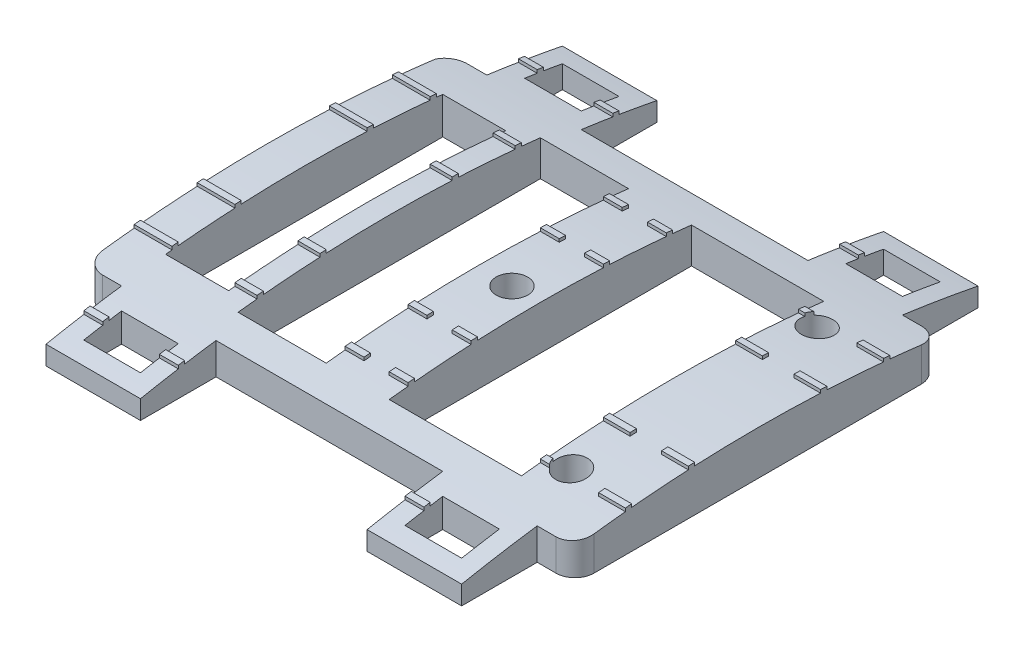
SolidWorks part; units mm, degrees
ref_plane "Front Plane" through (0, 0, 0) normal (0, 0, 1) x (1, 0, 0)
ref_plane "Top Plane" through (0, 0, 0) normal (0, 1, 0) x (1, 0, 0)
ref_plane "Right Plane" through (0, 0, 0) normal (1, 0, 0) x (0, 0, -1)
sketch "Sketch1" plane through (0, 0, 0) normal (0, 1, 0) x (1, 0, 0)
  line L0 (-33, -29) -> (-33, -41) construction
  line L5 (-33, -41) -> (-18, -41) construction
  line L6 (-18, -29) -> (-18, -41) construction
  line L7 (18, -29) -> (18, -41) construction
  line L8 (33, -41) -> (18, -41) construction
  line L9 (33, -29) -> (33, -41) construction
  line L10 (18, 29) -> (18, 41) construction
  line L11 (33, 41) -> (18, 41) construction
  line L12 (33, 29) -> (33, 41) construction
  line L13 (-33, 29) -> (-33, 41) construction
  line L14 (-33, 41) -> (-18, 41) construction
  line L15 (-18, 29) -> (-18, 41) construction
  line L16 (-36.1131, 29) -> (-33, 29) construction
  line L17 (-33, 29) -> (-18, 29) construction
  line L18 (-18, 29) -> (18, 29) construction
  line L19 (18, 29) -> (33, 29) construction
  line L20 (33, 29) -> (36, 29) construction
  line L21 (-36, -29) -> (-33, -29) construction
  line L34 (-18, -29) -> (-33, -29) construction
  line L35 (-18, -29) -> (18, -29) construction
  line L36 (33, -29) -> (18, -29) construction
  line L38 (33, -29) -> (36, -29) construction
  line L40 (-33, -29) -> (-33, -41)
  line L44 (-33, -41) -> (-18, -41)
  line L45 (-18, -29) -> (-18, -41)
  line L49 (18, -29) -> (18, -41)
  line L60 (33, -41) -> (18, -41)
  line L94 (33, -29) -> (33, -41)
  line L95 (18, 29) -> (18, 41)
  line L96 (33, 41) -> (18, 41)
  line L97 (33, 29) -> (33, 41)
  line L98 (-33, 29) -> (-33, 41)
  line L99 (-33, 41) -> (-18, 41)
  line L100 (-18, 29) -> (-18, 41)
  line L101 (-36.1131, 29) -> (-33, 29)
  line L102 (-33, 29) -> (-18, 29)
  line L103 (-18, 29) -> (18, 29)
  line L104 (18, 29) -> (33, 29)
  line L105 (33, 29) -> (36, 29)
  line L106 (-36, -29) -> (-33, -29)
  line L107 (-18, -29) -> (-33, -29)
  line L108 (-18, -29) -> (18, -29)
  line L109 (33, -29) -> (18, -29)
  line L110 (33, -29) -> (36, -29)
  line L111 (-39, -26) -> (-39, 26.8161)
  line L112 (39, -26) -> (39, 26)
  line L113 (-30, -32) -> (-30, -38) construction
  line L114 (-30, -38) -> (-21, -38) construction
  line L115 (-21, -32) -> (-21, -38) construction
  line L116 (-30, -32) -> (-21, -32) construction
  line L117 (21, -32) -> (21, -38) construction
  line L118 (30, -38) -> (21, -38) construction
  line L119 (30, -32) -> (21, -32) construction
  line L120 (30, -32) -> (30, -38) construction
  line L121 (-30, 32) -> (-21, 32) construction
  line L122 (-30, 32) -> (-30, 38) construction
  line L123 (-30, 38) -> (-21, 38) construction
  line L124 (-21, 32) -> (-21, 38) construction
  line L125 (21, 32) -> (21, 38) construction
  line L126 (30, 32) -> (21, 32) construction
  line L127 (30, 32) -> (30, 38) construction
  line L128 (30, 38) -> (21, 38) construction
  line L129 (-30, -32) -> (-30, -38)
  line L130 (-30, -38) -> (-21, -38)
  line L131 (-21, -32) -> (-21, -38)
  line L132 (-30, -32) -> (-21, -32)
  line L133 (21, -32) -> (21, -38)
  line L134 (30, -38) -> (21, -38)
  line L135 (30, -32) -> (21, -32)
  line L136 (30, -32) -> (30, -38)
  line L137 (-30, 32) -> (-21, 32)
  line L138 (-30, 32) -> (-30, 38)
  line L139 (-30, 38) -> (-21, 38)
  line L140 (-21, 32) -> (-21, 38)
  line L141 (21, 32) -> (21, 38)
  line L142 (30, 32) -> (21, 32)
  line L143 (30, 32) -> (30, 38)
  line L144 (30, 38) -> (21, 38)
  arc A0 (-36.1131, 29) -> (-39.0792, 26.45) centre (-36.1131, 26) ccw construction
  arc A1 (39, 26) -> (36, 29) centre (36, 26) ccw construction
  arc A2 (-39, -26) -> (-36, -29) centre (-36, -26) ccw construction
  arc A3 (36, -29) -> (39, -26) centre (36, -26) ccw construction
  arc A6 (-36.1131, 29) -> (-39, 26.8161) centre (-36.1131, 26) ccw
  arc A7 (39, 26) -> (36, 29) centre (36, 26) ccw
  arc A8 (-39, -26) -> (-36, -29) centre (-36, -26) ccw
  arc A9 (36, -29) -> (39, -26) centre (36, -26) ccw
extrude "Boss-Extrude1" add sketch "Sketch1" along normal blind 10
sketch "Sketch7" plane through (0, 0, 0) normal (0, -1, 0) x (1, 0, 0)
  circle A1 centre (28.95, 19.5) radius 2.5
  circle A3 centre (28.95, -19.5) radius 2.5
  circle A5 centre (0, 0) radius 2.5
  circle A8 centre (0, 0) radius 2 construction
  dimension "D1" = 0.5
extrude "Cut-Extrude6" cut sketch "Sketch7" against normal through all
sketch "Sketch8" plane through (0, 0, 0) normal (0, -1, 0) x (1, 0, 0)
  line L0 (-24, 21) -> (-32, -21) construction
  line L1 (-24, 21) -> (-32, 21) construction
  line L2 (-24, 21) -> (-24, -21) construction
  line L3 (-24, -21) -> (-32, -21) construction
  line L4 (-32, 21) -> (-32, -21) construction
  line L5 (-24, 21) -> (-32, -21) construction
  line L6 (-24, -21) -> (-32, 21) construction
  line L7 (5.5, -23) -> (24.5, 23) construction
  line L8 (-6.5, 23) -> (-18.5, 23) construction
  line L9 (-6.5, 23) -> (-6.5, -23) construction
  line L10 (-6.5, -23) -> (-18.5, -23) construction
  line L11 (-18.5, 23) -> (-18.5, -23) construction
  line L12 (-6.5, 23) -> (-18.5, -23) construction
  line L13 (-6.5, -23) -> (-18.5, 23) construction
  line L14 (24.5, 23) -> (5.5, 23) construction
  line L15 (24.5, 23) -> (24.5, -23) construction
  line L16 (24.5, -23) -> (5.5, -23) construction
  line L17 (5.5, 23) -> (5.5, -23) construction
  line L18 (24.5, 23) -> (5.5, -23) construction
  line L19 (24.5, -23) -> (5.5, 23) construction
  line L20 (25.5, -24) -> (4.5, -24)
  line L21 (4.5, 24) -> (4.5, -24)
  line L22 (25.5, 24) -> (4.5, 24)
  line L23 (25.5, 24) -> (25.5, -24)
  line L24 (-5.5, -24) -> (-19.5, -24)
  line L25 (-19.5, 24) -> (-19.5, -24)
  line L26 (-5.5, 24) -> (-19.5, 24)
  line L27 (-5.5, 24) -> (-5.5, -24)
  line L28 (-23, -22) -> (-33, -22)
  line L29 (-33, 22) -> (-33, -22)
  line L30 (-23, 22) -> (-33, 22)
  line L31 (-23, 22) -> (-23, -22)
  point P0 (-28, 0)
  point P8 (-12.5, 0)
  point P15 (15, 0)
  dimension "D1" = 1
extrude "Cut-Extrude7" cut sketch "Sketch8" against normal through all
sketch "Sketch11" plane through (-39, 0, 0) normal (-1, 0, 0) x (0, 0, 1)
  line L0 (-41, 10) -> (-41, 0) construction
  line L1 (41, 10) -> (41, 0) construction
  line L2 (-41, 3) -> (-41, 10)
  line L3 (-41, 10) -> (41, 10)
  line L4 (41, 10) -> (41, 3)
  line L5 (-34.9867, 4.0949) -> (-34.9867, 4.5949)
  line L6 (-34.9867, 4.5949) -> (-34, 4.7575)
  line L7 (-34, 4.7575) -> (-34, 4.2575)
  line L8 (-20.9953, 5.9584) -> (-20.9953, 6.4584)
  line L9 (-20.9953, 6.4584) -> (-20, 6.5551)
  line L10 (-20, 6.5551) -> (-20, 6.0551)
  line L11 (-10.9988, 6.7147) -> (-10.9988, 7.2147)
  line L12 (-10.9988, 7.2147) -> (-10, 7.2642)
  line L13 (-10, 7.2642) -> (-10, 6.7642)
  line L14 (0, 0) -> (0, 10) construction
  line L15 (34, 4.7575) -> (34, 4.2575)
  line L16 (34.9867, 4.5949) -> (34, 4.7575)
  line L17 (34.9867, 4.0949) -> (34.9867, 4.5949)
  line L18 (20, 6.5551) -> (20, 6.0551)
  line L19 (20.9953, 6.4584) -> (20, 6.5551)
  line L20 (20.9953, 5.9584) -> (20.9953, 6.4584)
  line L21 (10, 7.2642) -> (10, 6.7642)
  line L22 (10.9988, 6.7147) -> (10.9988, 7.2147)
  line L23 (10.9988, 7.2147) -> (10, 7.2642)
  arc A0 (-41, 3) -> (41, 3) centre (0, -205.125) cw
  point P12 (0, 7)
  line M13 (26, 0) -> (26, 10)
  line M14 (26, 10) -> (-26.8161, 10)
  line M15 (-26.8161, 10) -> (-26.8161, 0)
  dimension "D2" = 3
  dimension "D1" = 7
  dimension "D3" = 1
  dimension "D4" = 0.5
  dimension "D5" = 10
  dimension "D6" = 20
  dimension "D7" = 34
extrude "Cut-Extrude8" cut sketch "Sketch11" against normal through all contours L2 A0 L5 L6 L7 L8 L9 L10 L3 M15 | A0 L14 L3 L11 L12 L13 M15 | L14 A0 L21 L23 L22 M13 M14 | A0 L18 L19 L20 L15 L16 L17 L4 L3 M13
ref_plane "Plane1" through (-0.5, 0, 0) normal (-1, 0, 0) x (0, 0, 1)
sketch "Sketch12" plane through (-0.5, 0, 0) normal (-1, 0, 0) x (0, 0, 1)
  line L0 (-41, 3) -> (-41, 10.5171)
  line L1 (-41, 10.5171) -> (41, 10.5171)
  line L2 (41, 10.5171) -> (41, 3)
  arc A0 (-41, 3) -> (41, 3) centre (0, -205.125) cw
  arc A1 (-29, 5.0083) -> (-34, 4.2575) centre (0, -205.125) ccw construction
extrude "Cut-Extrude9" cut sketch "Sketch12" against normal mid plane 4
ref_plane "Plane2" through (32.25, 0, 0) normal (-1, 0, 0) x (0, 0, 1)
sketch "Sketch13" plane through (32.25, 0, 0) normal (-1, 0, 0) x (0, 0, 1)
  line L0 (-41, 3) -> (-41, 10.5171)
  line L1 (-41, 10.5171) -> (41, 10.5171)
  line L2 (41, 10.5171) -> (41, 3)
  arc A0 (-41, 3) -> (41, 3) centre (0, -205.125) cw
extrude "Cut-Extrude10" cut sketch "Sketch13" against normal mid plane 5
